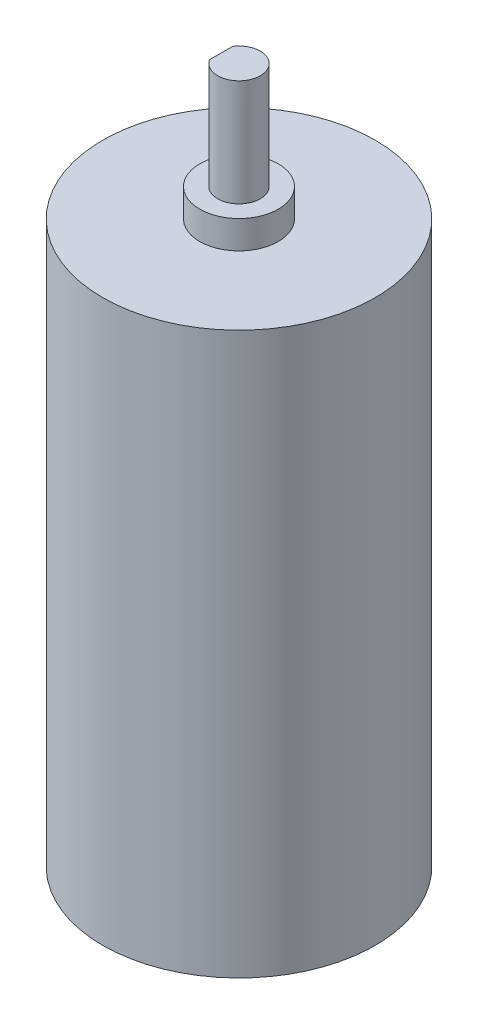
SolidWorks part; units mm, degrees
ref_plane "Front Plane" through (0, 0, 0) normal (0, 0, 1) x (1, 0, 0)
ref_plane "Top Plane" through (0, 0, 0) normal (0, 1, 0) x (1, 0, 0)
ref_plane "Right Plane" through (0, 0, 0) normal (1, 0, 0) x (0, 0, -1)
sketch "Sketch1" plane through (0, 0, 0) normal (0, 1, 0) x (1, 0, 0)
  circle A0 centre (0, 0) radius 12.15
  dimension "D1" = 24.3
extrude "Boss-Extrude1" add sketch "Sketch1" along normal blind 50
sketch "Sketch2" plane through (0, 50, 0) normal (0, 1, 0) x (1, 0, 0)
  circle A0 centre (0, 0) radius 3.5
  dimension "D1" = 7
extrude "Boss-Extrude2" add sketch "Sketch2" along normal blind 2.5
sketch "Sketch3" plane through (0, 52.5, 0) normal (0, 1, 0) x (1, 0, 0)
  line L0 (1.9014, 2.9385) -> (1.9014, -2.9385) construction
  line L1 (-1.5986, 1.0294) -> (-1.5986, -1.0294)
  arc A0 (-1.5986, -1.0294) -> (-1.5986, 1.0294) centre (0, 0) ccw
  circle A1 centre (0, 0) radius 3.5 construction
  circle A2 centre (0, 0) radius 3.5 construction
  dimension "D2" = 1.9014
  dimension "D1" = 3.5
extrude "Boss-Extrude3" add sketch "Sketch3" along normal blind 9.5
sketch "Sketch4" plane through (0, 52.5, 0) normal (0, 1, 0) x (1, 0, 0)
  circle A0 centre (0, 0) radius 1.9014
  arc A1 (-1.5986, -1.0294) -> (-1.5986, 1.0294) centre (0, 0) ccw construction
extrude "Boss-Extrude4" add sketch "Sketch4" along normal blind 1.5
